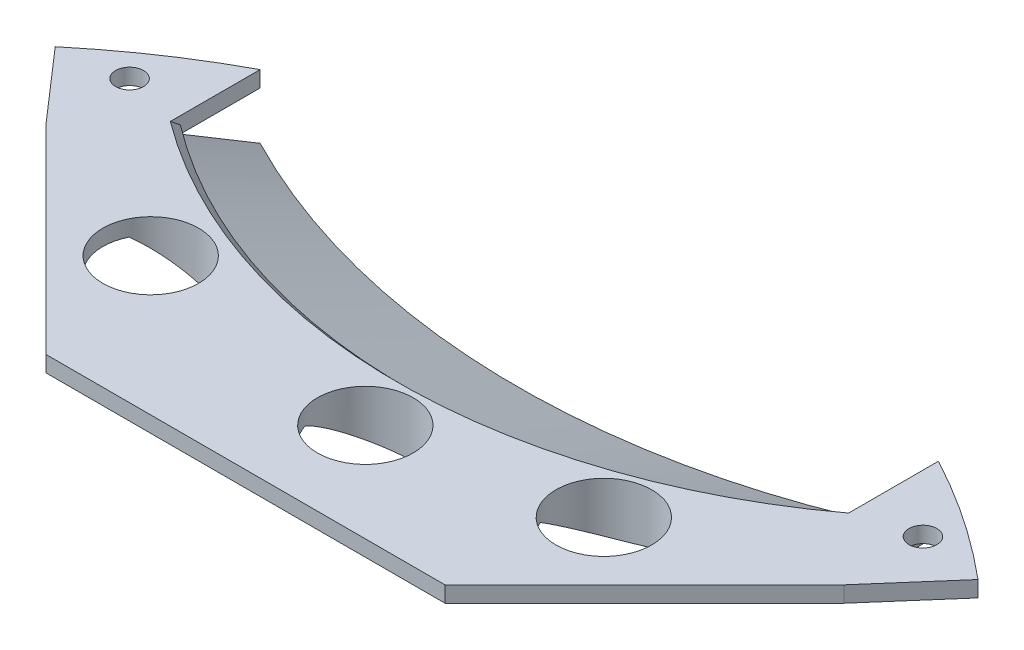
SolidWorks part; units mm, degrees
ref_plane "Front Plane" through (0, 0, 0) normal (0, 0, 1) x (1, 0, 0)
ref_plane "Top Plane" through (0, 0, 0) normal (0, 1, 0) x (1, 0, 0)
ref_plane "Right Plane" through (0, 0, 0) normal (1, 0, 0) x (0, 0, -1)
sketch "Sketch1" plane through (0, 0, 0) normal (0, 1, 0) x (1, 0, 0)
  circle A0 centre (0, 0) radius 90
extrude "Boss-Extrude1" add sketch "Sketch1" along normal blind 2
sketch "Sketch4" plane through (0, 2, 0) normal (0, 1, 0) x (1, 0, 0)
  line L0 (0, 90) -> (0, 55) construction
  line L1 (-42.5, 79.3332) -> (-42.5, 69.3332)
  line L2 (42.5, 79.3332) -> (42.5, 69.3332)
  line L3 (-42.5, 79.3332) -> (-42.5, 105.8098)
  line L4 (-42.5, 105.8098) -> (42.5, 105.8098)
  line L5 (42.5, 105.8098) -> (42.5, 79.3332)
  circle A0 centre (0, 0) radius 90 construction
  arc A1 (-42.5, 69.3332) -> (42.5, 69.3332) centre (0, 125.1761) ccw
  circle A5 centre (0, 0) radius 90 construction
  dimension "D1" = 35
  dimension "D2" = 42.5
  dimension "D3" = 42.5
  dimension "D4" = 10
  dimension "D5" = 10
extrude "Cut-Extrude2" cut sketch "Sketch4" against normal through all
sketch "Sketch9" plane through (0, 2, 0) normal (0, 1, 0) x (1, 0, 0)
  circle A0 centre (-49.7064, 70.1803) radius 1.75
  arc A1 (-42.5, 79.3332) -> (42.5, 79.3332) centre (0, 0) ccw construction
  dimension "D2" = 3.5
  dimension "D1" = 86
extrude "Cut-Extrude7" cut sketch "Sketch9" against normal through all
mirror "Mirror1" about plane through (0, 0, 0) normal (1, 0, 0) of "Cut-Extrude7"
sketch "Sketch10" plane through (0, 0, 0) normal (0, -1, 0) x (1, 0, 0)
  line L0 (57.8174, -68.9721) -> (50, -60)
  line L1 (50, -60) -> (25, -35)
  line L2 (25, -35) -> (-25, -35)
  line L3 (-25, -35) -> (-50, -60)
  line L4 (-50, -60) -> (-57.8174, -68.9721)
  line L5 (0, 0) -> (0, -35) construction
  arc A0 (42.5, -79.3332) -> (-42.5, -79.3332) centre (0, 0) ccw construction
  dimension "D1" = 35
  dimension "D2" = 25
  dimension "D3" = 25
  dimension "D5" = 25
  dimension "D7" = 25
  dimension "D8" = 11.9
  dimension "D9" = 11.9
extrude "Cut-Extrude8" cut sketch "Sketch10" along direction (0, 1, 0) on the side against the normal through all and the other way through all flip side to cut
ref_plane "Plane1" through (0, -6, 0) normal (0, 1, 0) x (1, 0, 0)
sketch "Sketch15" plane through (0, -6, 0) normal (0, 1, 0) x (1, 0, 0)
  line L0 (-42.5, 69.3332) -> (-42.5, 79.3332)
  line L1 (42.5, 69.3332) -> (42.5, 79.3332)
  arc A0 (-42.5, 79.3332) -> (42.5, 79.3332) centre (0, 161.8761) ccw
  arc A1 (-42.5, 69.3332) -> (42.5, 69.3332) centre (0, 125.1761) ccw
sketch "Sketch16" plane through (0, 0, 0) normal (0, -1, 0) x (1, 0, 0)
  line L0 (-45.9485, -63.852) -> (-42.5, -69.3332)
  line L1 (44.152, -63.852) -> (42.5, -69.3332)
  arc A0 (-42.5, -69.3332) -> (42.5, -69.3332) centre (0, -125.1761) cw
  arc A1 (-45.9485, -63.852) -> (44.152, -63.852) centre (-0.8982, -109.7669) cw
loft "Loft1" add profiles "Sketch15", "Sketch16"
chamfer "Chamfer3" distance 1 angle 45 1 edges at (0, 2, -55)
sketch "Sketch17" plane through (0, 2, 0) normal (0, 1, 0) x (1, 0, 0)
  circle A0 centre (2.6977, 47.316) radius 6
  circle A1 centre (27.6286, 52.2741) radius 6
  circle A2 centre (-29.1519, 52.2741) radius 6
  dimension "D1" = 12
  dimension "D2" = 12
  dimension "D3" = 12
extrude "Cut-Extrude9" cut sketch "Sketch17" against normal through all
